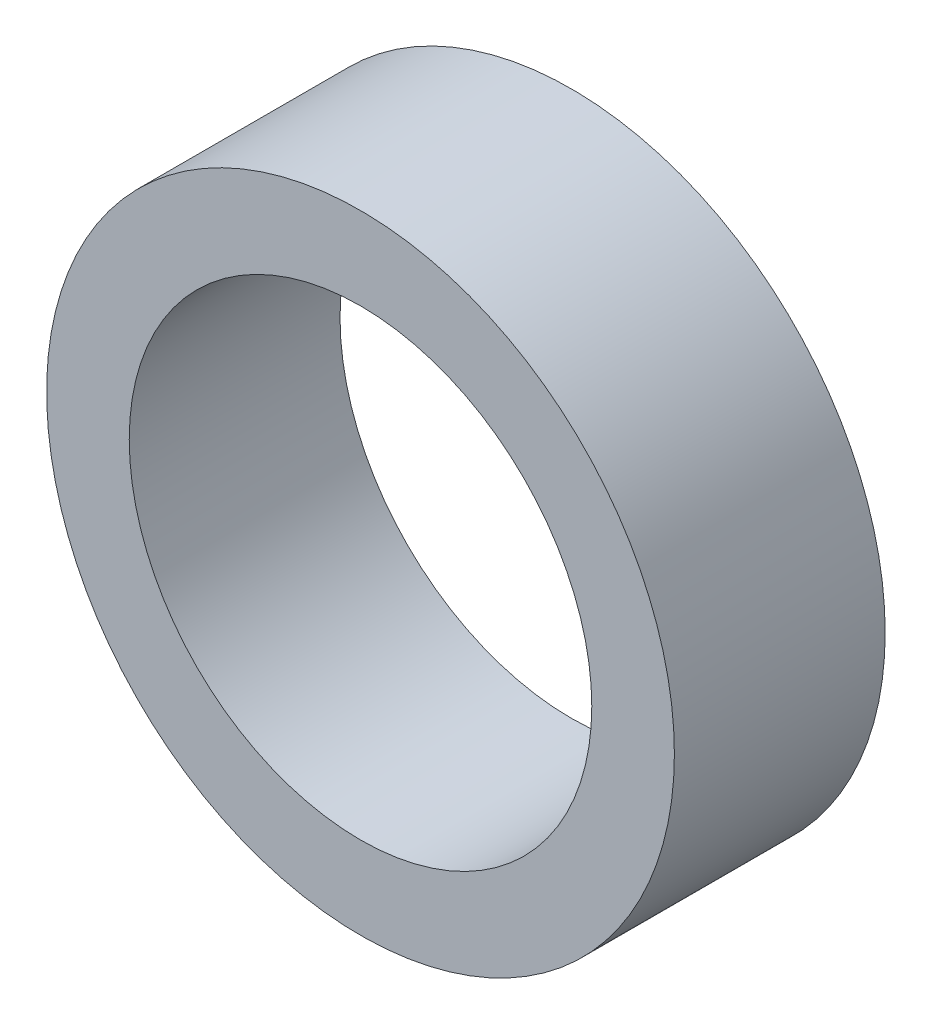
SolidWorks part; units mm, degrees
ref_plane "Front Plane" through (0, 0, 0) normal (0, 0, 1) x (1, 0, 0)
ref_plane "Top Plane" through (0, 0, 0) normal (0, 1, 0) x (1, 0, 0)
ref_plane "Right Plane" through (0, 0, 0) normal (1, 0, 0) x (0, 0, -1)
sketch "Sketch1" plane through (0, 0, 0) normal (0, 0, 1) x (1, 0, 0)
  circle A0 centre (0, 0) radius 4.826
  circle A1 centre (0, 0) radius 3.556
  dimension "D1" = 7.112
  dimension "D2" = 1.27
extrude "Boss-Extrude1" add sketch "Sketch1" along normal blind 3.241
